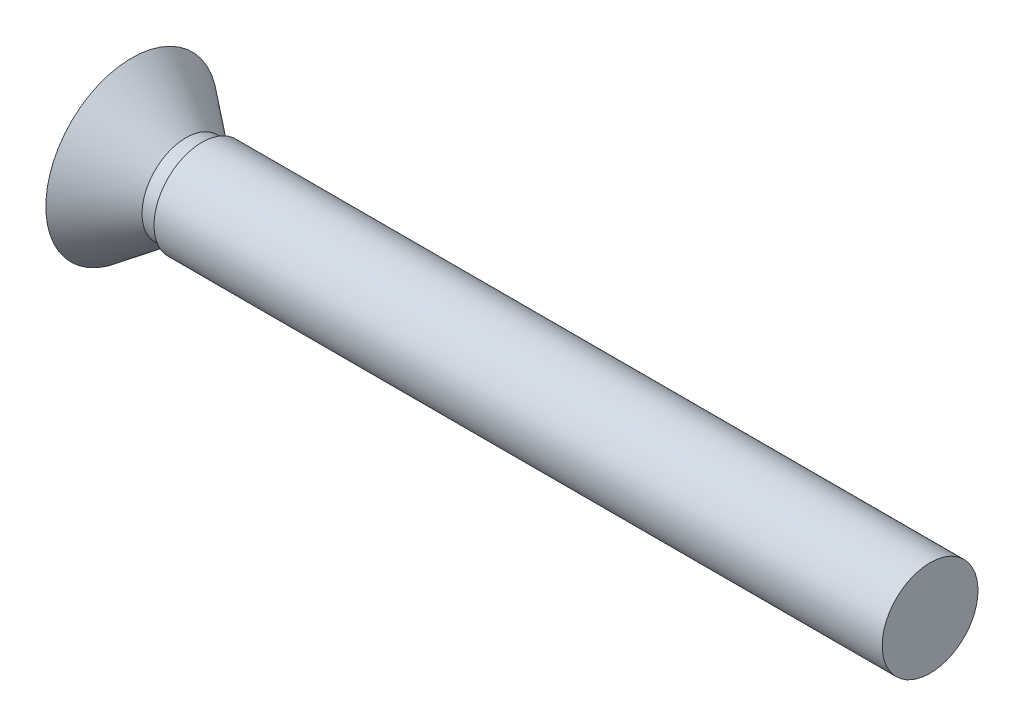
SolidWorks part; units mm, degrees
ref_plane "Front Plane" through (0, 0, 0) normal (0, 0, 1) x (1, 0, 0)
ref_plane "Top Plane" through (0, 0, 0) normal (0, 1, 0) x (1, 0, 0)
ref_plane "Right Plane" through (0, 0, 0) normal (1, 0, 0) x (0, 0, -1)
sketch "Sketch2" plane through (0, 0, 0) normal (0, 1, 0) x (1, 0, 0)
  line L0 (0, 0) -> (-46.6, 0)
  line L1 (0, 0) -> (0, 3)
  line L3 (-46.6, 2.75) -> (-50, 5.375)
  line L4 (-50, 5.375) -> (-50, 0)
  line L6 (-46.6, 0) -> (-50, 0)
  line L7 (0, 3) -> (-45.6, 3)
  line L8 (-45.6, 3) -> (-45.6, 2.75)
  line L9 (-45.6, 2.75) -> (-46.6, 2.75)
  dimension "D1" = 3
  dimension "D2" = 3.4
  dimension "D3" = 50
  dimension "D4" = 5.375
  dimension "D5" = 2.75
  dimension "D6" = 1
revolve "Revolve1" add sketch "Sketch2" angle 360 about L0
